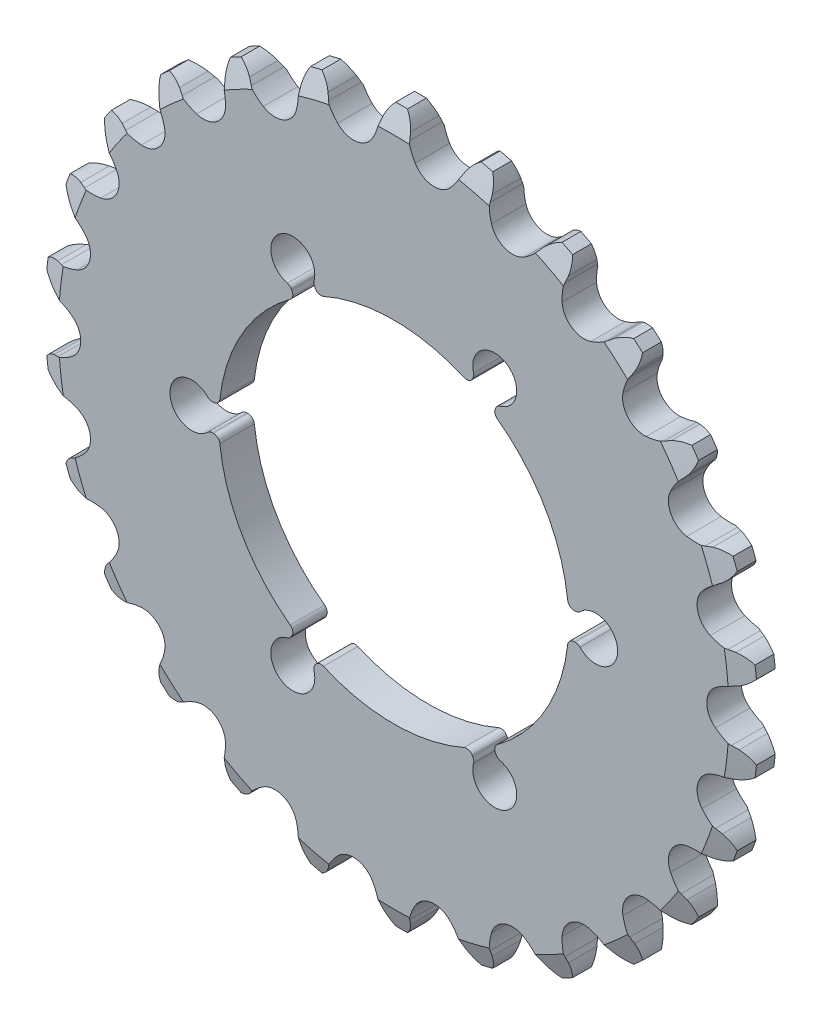
SolidWorks part; units mm, degrees
material "6063-O"
ref_plane "Front Plane" through (0, 0, 0) normal (0, 0, 1) x (1, 0, 0)
ref_plane "Top Plane" through (0, 0, 0) normal (0, 1, 0) x (1, 0, 0)
ref_plane "Right Plane" through (0, 0, 0) normal (1, 0, 0) x (0, 0, -1)
sketch "Sketch1" plane through (0, 0, 0) normal (0, 0, 1) x (1, 0, 0)
  circle A0 centre (0, 0) radius 42.0802
  circle A1 centre (0, 0) radius 20.6375
  dimension "D1" = 84.1604
  dimension "D2" = 41.275
extrude "Extrude1" add sketch "Sketch1" along normal mid plane 4.064
sketch "Sketch2" plane through (0, 0, 0) normal (0, 0, 1) x (1, 0, 0)
  line L0 (0, 0) -> (0, 30.7585) construction
  line L1 (11.9062, 20.6222) -> (0, 0) construction
  line L2 (8.9134, 18.6134) -> (9.5077, 19.6428)
  line L3 (12.2573, 18.0553) -> (11.663, 17.0259)
  arc A0 (12.2573, 18.0553) -> (9.5077, 19.6428) centre (11.9062, 20.6222) ccw
  circle A1 centre (0, 0) radius 20.6375 construction
  arc A2 (11.663, 17.0259) -> (8.9134, 18.6134) centre (0, 0) ccw
  dimension "D1" = 5.1816
  dimension "D2" = 23.8125
  dimension "D3" = 30
  dimension "D4" = 3.175
extrude "Extrude2" cut sketch "Sketch2" against normal through all and the other way through all
pattern_circular "CirPattern1" count 6 over 360 about axis through (0, 0, 0) along (0, 0, 1) of "Extrude2"
chamfer "Chamfer1" distance 2.54 angle 20 1 edges at (42.0802, 0, 2.032)
chamfer "Chamfer2" distance 2.54 angle 20 1 edges at (42.0802, 0, -2.032)
sketch "Sketch3" plane through (0, 0, 0) normal (0, 0, 1) x (1, 0, 0)
  line L0 (0, 0) -> (4.7625, 39.2227) construction
  line L1 (0, 0) -> (0, 51.8431) construction
  line L2 (1.7836, 39.7994) -> (1.6302, 40.4779)
  line L3 (8.1042, 39.6919) -> (7.7928, 39.0697)
  circle A0 centre (0, 0) radius 42.0802 construction
  circle A1 centre (0, 0) radius 42.0802 construction
  arc A2 (9.3909, 41.0189) -> (0.6985, 42.0744) centre (0, 0) ccw
  arc A5 (1.7836, 39.7994) -> (2.5239, 37.9184) centre (8.2695, 41.266) ccw
  arc A6 (2.5239, 37.9184) -> (6.6239, 37.4206) centre (4.7625, 39.2227) ccw
  arc A7 (1.6302, 40.4779) -> (0.6985, 42.0744) centre (-2.351, 39.2246) ccw
  arc A8 (6.6239, 37.4206) -> (7.7928, 39.0697) centre (1.8464, 42.0459) ccw
  arc A9 (9.3909, 41.0189) -> (8.1042, 39.6919) centre (11.6698, 37.5222) ccw
  dimension "D1" = 2.5908
  dimension "D2" = 6.6497
  dimension "D4" = 4.1738
  dimension "D7" = 6.5216
  dimension "D6" = 10.815
  dimension "D3" = 39.33
  dimension "D5" = 1.397
  dimension "D9" = 39.5108
  dimension "D10" = 6.923
extrude "Extrude3" cut sketch "Sketch3" against normal through all and the other way through all
pattern_circular "CirPattern2" count 26 over 360 about axis through (0, 0, 0) along (0, 0, 1) of "Extrude3"
fillet "Fillet1" radius 0.762 24 edges at (21.765, 1.5875, 0) (20.5764, 1.5875, 0) (21.765, -1.5875, 0) (20.5764, -1.5875, 0) (11.663, -17.0259, 0) (12.2573, -18.0553, 0) (8.9134, -18.6134, 0) (9.5077, -19.6428, 0) (-8.9134, -18.6134, 0) (-9.5077, -19.6428, 0) (-11.663, -17.0259, 0) (-12.2573, -18.0553, 0) (-20.5764, -1.5875, 0) (-21.765, -1.5875, 0) (-20.5764, 1.5875, 0) (-21.765, 1.5875, 0) (-11.663, 17.0259, 0) (-12.2573, 18.0553, 0) (-9.5077, 19.6428, 0) (-8.9134, 18.6134, 0) (9.5077, 19.6428, 0) (8.9134, 18.6134, 0) (12.2573, 18.0553, 0) (11.663, 17.0259, 0)
sketch "Sketch4" plane through (0, 0, 0) normal (0, 0, 1) x (1, 0, 0)
  circle A0 centre (0, 0) radius 39.5108
